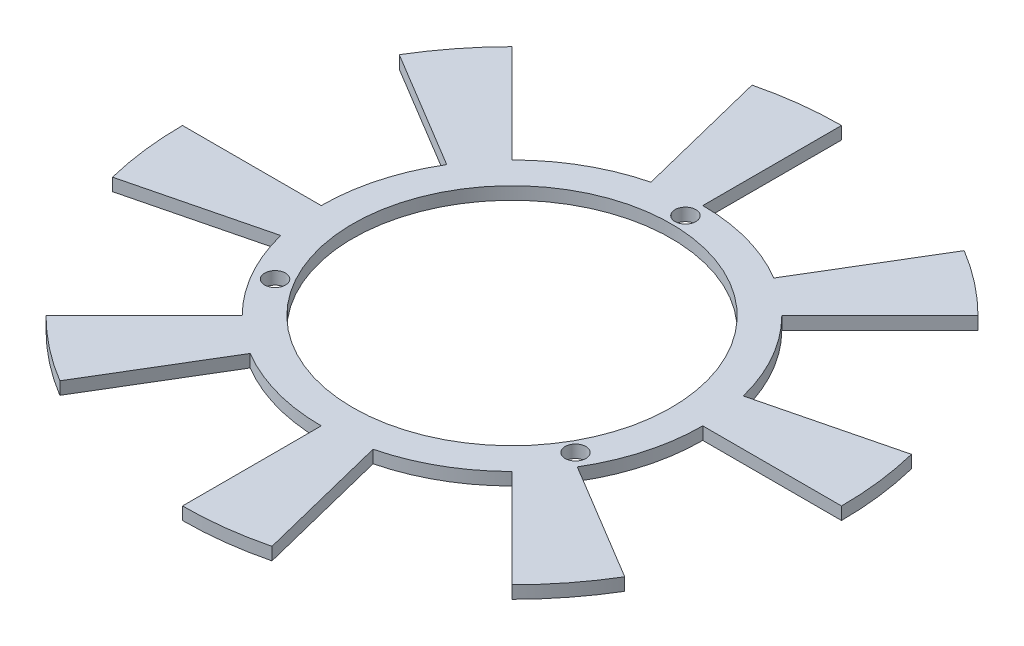
SolidWorks part; units mm, degrees
material "AISI 1010 Steel, hot rolled bar"
ref_plane "Front Plane" through (0, 0, 0) normal (0, 0, 1) x (1, 0, 0)
ref_plane "Top Plane" through (0, 0, 0) normal (0, 1, 0) x (1, 0, 0)
ref_plane "Right Plane" through (0, 0, 0) normal (1, 0, 0) x (0, 0, -1)
sketch "Sketch1" plane through (0, 0, 0) normal (0, 1, 0) x (1, 0, 0)
  circle A0 centre (0, 0) radius 25.25
  dimension "D1" = 50.5
extrude "Extrude-Thin1" add sketch "Sketch1" against normal blind 2 thin
sketch "Sketch2" plane through (0, 0, 0) normal (0, 1, 0) x (1, 0, 0)
  line L0 (0, -30.25) -> (0, 30.25) construction
  line L1 (0, 0) -> (23.8157, -13.75) construction
  line L2 (0, 0) -> (-23.8157, -13.75) construction
  circle A0 centre (0, 27.5) radius 1.65
  circle A1 centre (0, 0) radius 30.25 construction
  circle A4 centre (0, 0) radius 27.5 construction
  circle A7 centre (23.8157, -13.75) radius 1.65
  circle A8 centre (-23.8157, -13.75) radius 1.65
  dimension "D1" = 55
  dimension "D2" = 3.3
  dimension "D3" = 120
  dimension "D4" = 120
extrude "Cut-Extrude3" cut sketch "Sketch2" against normal blind 10
sketch "Sketch5" plane through (0, -2, 0) normal (0, -1, 0) x (1, 0, 0)
  line L0 (0, 0) -> (0, 35.9971) construction
  line L1 (0, 0) -> (8.2512, 33.0937) construction
  line L2 (0, 52.25) -> (0, 30.25)
  line L3 (7.3181, 29.3514) -> (12.6404, 50.698)
  line L4 (36.9463, 36.9463) -> (21.39, 21.39)
  line L5 (25.9293, 15.5799) -> (44.787, 26.9107)
  line L6 (52.25, 0) -> (30.25, 0)
  line L7 (29.3514, -7.3181) -> (50.698, -12.6404)
  line L8 (36.9463, -36.9463) -> (21.39, -21.39)
  line L9 (15.5799, -25.9293) -> (26.9107, -44.787)
  line L10 (0, -52.25) -> (0, -30.25)
  line L11 (-7.3181, -29.3514) -> (-12.6404, -50.698)
  line L12 (-36.9463, -36.9463) -> (-21.39, -21.39)
  line L13 (-25.9293, -15.5799) -> (-44.787, -26.9107)
  line L14 (-52.25, 0) -> (-30.25, 0)
  line L15 (-29.3514, 7.3181) -> (-50.698, 12.6404)
  line L16 (-36.9463, 36.9463) -> (-21.39, 21.39)
  line L17 (-15.5799, 25.9293) -> (-26.9107, 44.787)
  circle A0 centre (0, 0) radius 30.25 construction
  arc A1 (7.3181, 29.3514) -> (0, 30.25) centre (0, 0) ccw
  arc A2 (12.6404, 50.698) -> (0, 52.25) centre (0, 0) ccw
  arc A3 (44.787, 26.9107) -> (36.9463, 36.9463) centre (0, 0) ccw
  arc A4 (25.9293, 15.5799) -> (21.39, 21.39) centre (0, 0) ccw
  arc A5 (50.698, -12.6404) -> (52.25, 0) centre (0, 0) ccw
  arc A6 (29.3514, -7.3181) -> (30.25, 0) centre (0, 0) ccw
  arc A7 (26.9107, -44.787) -> (36.9463, -36.9463) centre (0, 0) ccw
  arc A8 (15.5799, -25.9293) -> (21.39, -21.39) centre (0, 0) ccw
  arc A9 (-12.6404, -50.698) -> (0, -52.25) centre (0, 0) ccw
  arc A10 (-7.3181, -29.3514) -> (0, -30.25) centre (0, 0) ccw
  arc A11 (-44.787, -26.9107) -> (-36.9463, -36.9463) centre (0, 0) ccw
  arc A12 (-25.9293, -15.5799) -> (-21.39, -21.39) centre (0, 0) ccw
  arc A13 (-50.698, 12.6404) -> (-52.25, 0) centre (0, 0) ccw
  arc A14 (-29.3514, 7.3181) -> (-30.25, 0) centre (0, 0) ccw
  arc A15 (-26.9107, 44.787) -> (-36.9463, 36.9463) centre (0, 0) ccw
  arc A16 (-15.5799, 25.9293) -> (-21.39, 21.39) centre (0, 0) ccw
  point P87 (0, 0)
  dimension "D2" = 22
  dimension "D1" = 14
  dimension "D3" = 8
extrude "Boss-Extrude1" add sketch "Sketch5" against normal blind 2
